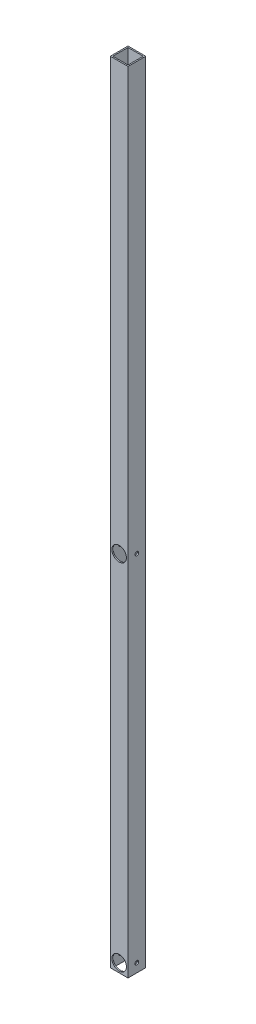
SolidWorks part; units mm, degrees
material "6063-T6"
ref_plane "Front Plane" through (0, 0, 0) normal (0, 0, 1) x (1, 0, 0)
ref_plane "Top Plane" through (0, 0, 0) normal (0, 1, 0) x (1, 0, 0)
ref_plane "Right Plane" through (0, 0, 0) normal (1, 0, 0) x (0, 0, -1)
sketch "Sketch1" plane through (0, 0, 0) normal (0, 1, 0) x (1, 0, 0)
  line L0 (41.275, 3.175) -> (41.275, 41.275)
  line L1 (0, 0) -> (44.45, 0)
  line L2 (0, 0) -> (0, 44.45)
  line L3 (0, 44.45) -> (44.45, 44.45)
  line L4 (44.45, 0) -> (44.45, 44.45)
  line L5 (3.175, 41.275) -> (41.275, 41.275)
  line L6 (3.175, 3.175) -> (3.175, 41.275)
  line L7 (3.175, 3.175) -> (41.275, 3.175)
  dimension "D1" = 44.45
  dimension "D2" = 3.175
extrude "Boss-Extrude1" add sketch "Sketch1" along normal blind 1981.2
sketch "Sketch2" plane through (0, 0, 0) normal (0, 0, 1) x (1, 0, 0)
  line L0 (0, 0) -> (44.45, 0) construction
  line L1 (44.45, 1981.2) -> (44.45, 0) construction
  circle A0 centre (22.225, 22.225) radius 18.2562
  circle A1 centre (22.225, 911.225) radius 18.2563
  dimension "D1" = 889
  dimension "D4" = 36.5125
  dimension "D2" = 22.225
  dimension "D3" = 22.225
extrude "Cut-Extrude1" cut sketch "Sketch2" against normal through all
sketch "Sketch3" plane through (44.45, 0, 0) normal (1, 0, 0) x (0, 0, -1)
  line L0 (44.45, 1981.2) -> (44.45, 0) construction
  line L1 (0, 0) -> (44.45, 0) construction
  circle A0 centre (22.225, 22.225) radius 4.7625
  circle A1 centre (22.225, 911.225) radius 4.7625
  dimension "D1" = 889
  dimension "D4" = 9.525
  dimension "D2" = 22.225
  dimension "D3" = 22.225
extrude "Cut-Extrude2" cut sketch "Sketch3" against normal through all
